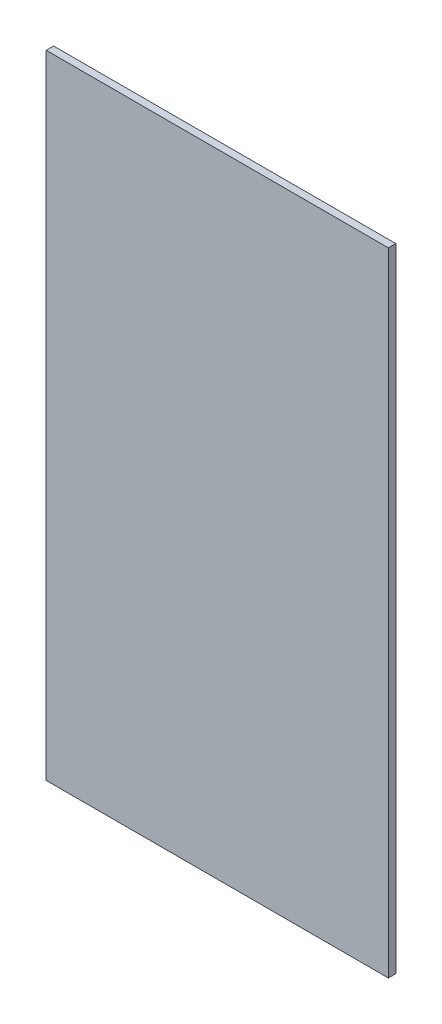
SolidWorks part; units mm, degrees
ref_plane "Front Plane" through (0, 0, 0) normal (0, 0, 1) x (1, 0, 0)
ref_plane "Top Plane" through (0, 0, 0) normal (0, 1, 0) x (1, 0, 0)
ref_plane "Right Plane" through (0, 0, 0) normal (1, 0, 0) x (0, 0, -1)
sketch "Sketch1" plane through (0, 0, 0) normal (0, 0, 1) x (1, 0, 0)
  line L2 (-115, 217.5) -> (-115, -207.5)
  line L3 (-115, -207.5) -> (115, -207.5)
  line L4 (115, -207.5) -> (115, 217.5)
  line L5 (115, 217.5) -> (-115, 217.5)
  dimension "D1" = 425
  dimension "D2" = 230
extrude "Boss-Extrude1" add sketch "Sketch1" along normal blind 5
